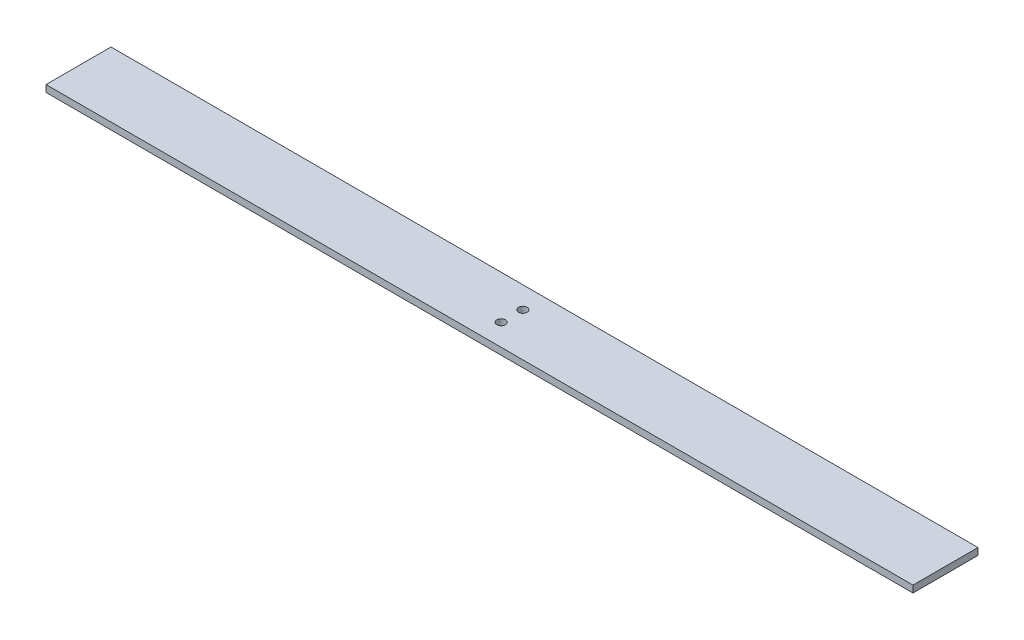
SolidWorks part; units mm, degrees
ref_plane "Front Plane" through (0, 0, 0) normal (0, 0, 1) x (1, 0, 0)
ref_plane "Top Plane" through (0, 0, 0) normal (0, 1, 0) x (1, 0, 0)
ref_plane "Right Plane" through (0, 0, 0) normal (1, 0, 0) x (0, 0, -1)
sketch "Sketch1" plane through (0, 0, 0) normal (0, 1, 0) x (1, 0, 0)
  line L1 (-175.9471, 39.699) -> (224.0529, 39.699)
  line L2 (-175.9471, 39.699) -> (-175.9471, 9.699)
  line L3 (-175.9471, 9.699) -> (224.0529, 9.699)
  line L4 (224.0529, 39.699) -> (224.0529, 9.699)
  dimension "D1" = 400
  dimension "D2" = 30
extrude "Boss-Extrude1" add sketch "Sketch1" along normal blind 3.175
sketch "Sketch2" plane through (0, 3.175, 0) normal (0, 1, 0) x (1, 0, 0)
  line L0 (24.0529, 39.699) -> (24.0529, 9.699) construction
  line L1 (224.0529, 39.699) -> (-175.9471, 39.699) construction
  line L2 (-175.9471, 9.699) -> (224.0529, 9.699) construction
  circle A0 centre (24.0529, 29.699) radius 2
  circle A1 centre (24.0529, 19.699) radius 2
  point P11 (24.0529, 24.699)
  dimension "D1" = 10
  dimension "D2" = 5
extrude "Cut-Extrude1" cut sketch "Sketch2" against normal blind 3.175
